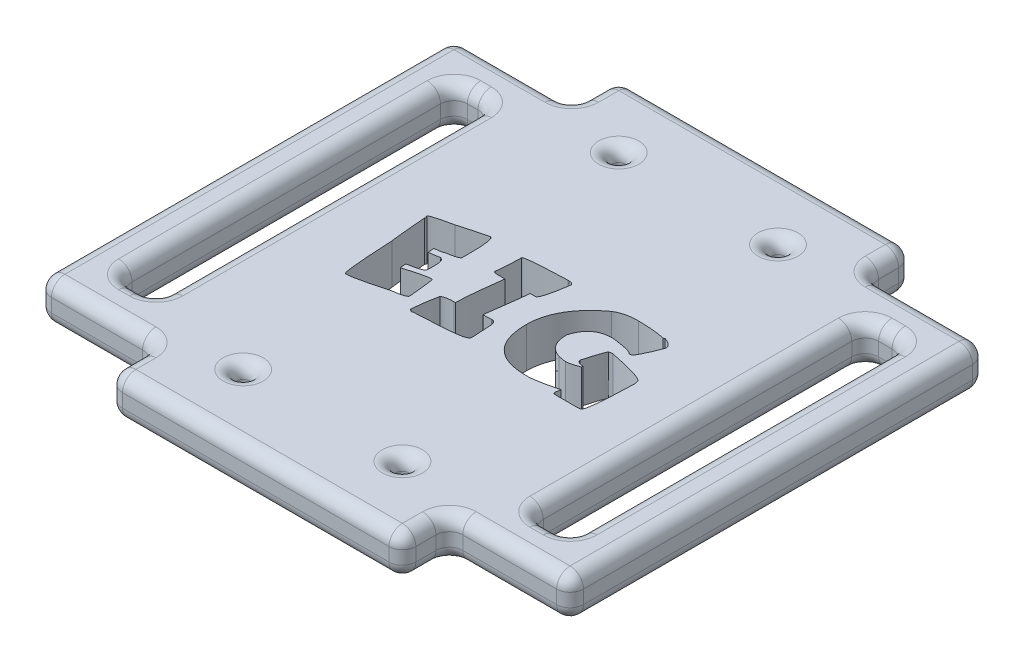
SolidWorks part; units mm, degrees
ref_plane "Front Plane" through (0, 0, 0) normal (0, 0, 1) x (1, 0, 0)
ref_plane "Top Plane" through (0, 0, 0) normal (0, 1, 0) x (1, 0, 0)
ref_plane "Right Plane" through (0, 0, 0) normal (1, 0, 0) x (0, 0, -1)
sketch "Sketch1" plane through (0, 0, 0) normal (0, 1, 0) x (1, 0, 0)
  line L1 (0, 0) -> (21.8718, 0)
  line L2 (0, 0) -> (0, 38)
  line L3 (0, 38) -> (21.8718, 38)
  line L4 (21.8718, 0) -> (21.8718, 38)
extrude "Boss-Extrude2" add sketch "Sketch1" along normal blind 3 contours L3 L4 L1 L2
sketch "Sketch8" plane through (0, 0, 0) normal (0, 1, 0) x (1, 0, 0)
  line L0 (0, 0) -> (0, 38) construction
  line L1 (0, 3.5) -> (-8.7888, 3.5)
  line L2 (0, 3.5) -> (0, 34.5)
  line L3 (0, 34.5) -> (-8.7888, 34.5)
  line L4 (-8.7888, 3.5) -> (-8.7888, 34.5)
  line L5 (21.8718, 0) -> (21.8718, 38) construction
  line L6 (-5.7888, 31.5) -> (-3, 31.5)
  line L7 (-5.7888, 31.5) -> (-5.7888, 6.5)
  line L8 (-5.7888, 6.5) -> (-3, 6.5)
  line L9 (-3, 31.5) -> (-3, 6.5)
  line L10 (21.8718, 3.5) -> (30.8718, 3.5)
  line L11 (21.8718, 3.5) -> (21.8718, 34.5)
  line L12 (21.8718, 34.5) -> (30.8718, 34.5)
  line L13 (30.8718, 3.5) -> (30.8718, 34.5)
  line L15 (24.8718, 31.5) -> (27.8718, 31.5)
  line L16 (24.8718, 31.5) -> (24.8718, 6.5)
  line L17 (24.8718, 6.5) -> (27.8718, 6.5)
  line L18 (27.8718, 31.5) -> (27.8718, 6.5)
  dimension "D1" = 25
  dimension "D2" = 3
  dimension "D3" = 3
  dimension "D4" = 3
  dimension "D5" = 3
  dimension "D6" = 3
  dimension "D7" = 3
  dimension "D8" = 3
  dimension "D9" = 3
  dimension "D10" = 25
  dimension "D11" = 3
  dimension "D12" = 3.5
  dimension "D13" = 3.5
  dimension "D14" = 3.5
extrude "Boss-Extrude5" add sketch "Sketch8" along normal blind 3
sketch "Sketch11" plane through (0, 3, 0) normal (0, 1, 0) x (1, 0, 0)
  circle A0 centre (5, 33) radius 0.5
  circle A1 centre (16.8718, 33) radius 0.5
  circle A2 centre (5, 5) radius 0.5
  circle A3 centre (16.8718, 5) radius 0.5
extrude "Cut-Extrude5" cut sketch "Sketch11" against normal blind 3
fillet "Fillet1" radius 1 68 edges at (26.3718, 0, -6.5) (26.3718, 3, -6.5) (26.3718, 0, -31.5) (26.3718, 3, -31.5) (-4.3944, 0, -31.5) (-4.3944, 3, -31.5) (-4.3944, 0, -6.5) (-4.3944, 3, -6.5) (27.8718, 1.5, -31.5) (27.8718, 1.5, -6.5) (27.8718, 0, -19) (27.8718, 3, -19) (24.8718, 1.5, -6.5) (24.8718, 1.5, -31.5) (24.8718, 0, -19) (24.8718, 3, -19) (-5.7888, 1.5, -6.5) (-5.7888, 1.5, -31.5) (-5.7888, 0, -19) (-5.7888, 3, -19) (-3, 1.5, -31.5) (-3, 1.5, -6.5) (-3, 0, -19) (-3, 3, -19) (0, 1.5, 0) (10.9359, 0, 0) (21.8718, 1.5, 0) (30.8718, 1.5, -3.5) (30.8718, 1.5, -34.5) (30.8718, 0, -19) (30.8718, 3, -19) (21.8718, 1.5, -38) (10.9359, 0, -38) (0, 1.5, -38) (-8.7888, 1.5, -34.5) (-8.7888, 1.5, -3.5) (-8.7888, 0, -19) (-8.7888, 3, -19) (10.9359, 3, -38) (10.9359, 3, 0) (5, 3, -32.5) (16.8718, 3, -32.5) (5, 3, -4.5) (16.8718, 3, -4.5) (5, 0, -32.5) (16.8718, 0, -32.5) (5, 0, -4.5) (16.8718, 0, -4.5)
sketch "Sketch12" plane through (0, 3, 0) normal (0, 1, 0) x (1, 0, 0)
  text T0 "EIG" font "Otaku Rant" height in points 32
extrude "Cut-Extrude6" cut sketch "Sketch12" against normal blind 3
